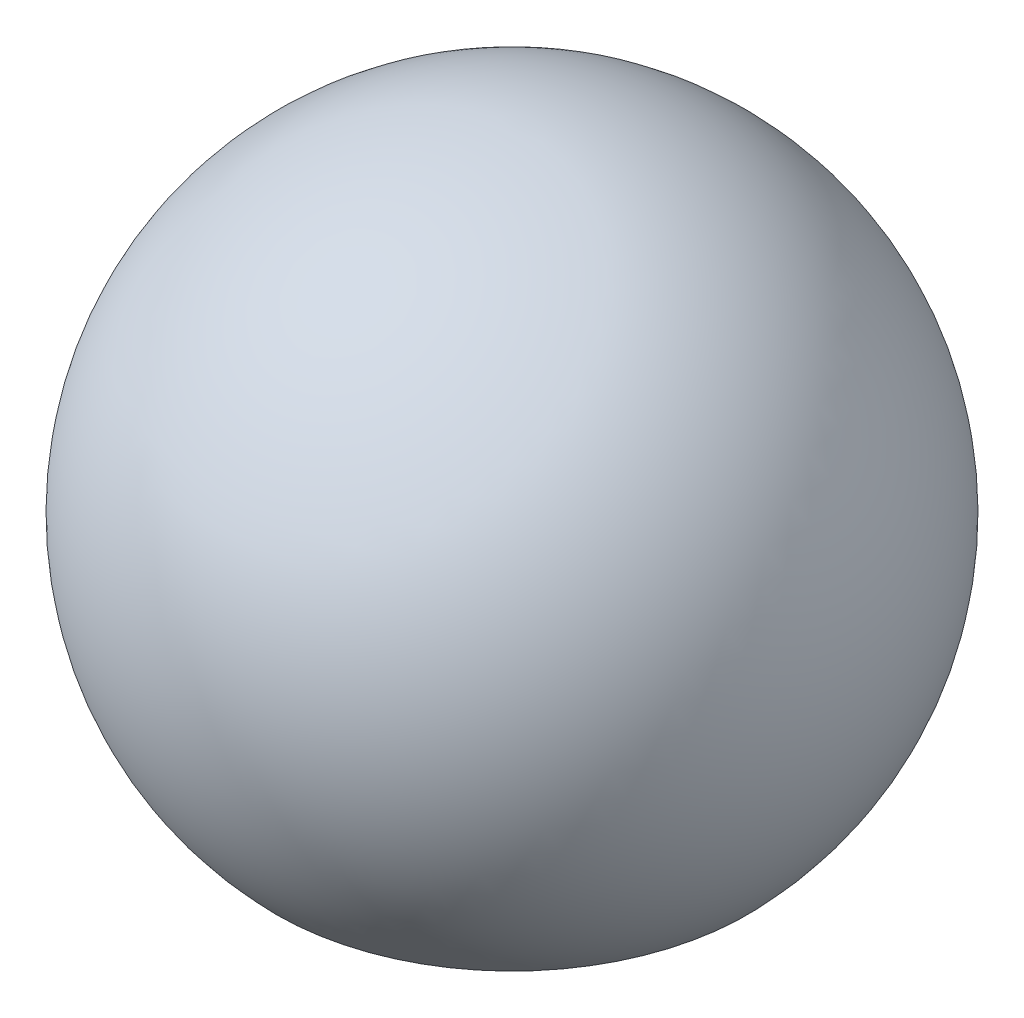
SolidWorks part; units mm, degrees
ref_plane "Front Plane" through (0, 0, 0) normal (0, 0, 1) x (1, 0, 0)
ref_plane "Top Plane" through (0, 0, 0) normal (0, 1, 0) x (1, 0, 0)
ref_plane "Right Plane" through (0, 0, 0) normal (1, 0, 0) x (0, 0, -1)
sketch "Sketch1" plane through (0, 0, 0) normal (0, 1, 0) x (1, 0, 0)
  line L0 (31.5004, 88.2413) -> (31.5004, 80.2413)
  arc A0 (31.5004, 88.2413) -> (31.5004, 80.2413) centre (31.5004, 84.2413) ccw
  dimension "D1" = 8
revolve "Revolve1" add sketch "Sketch1" angle 360 about L0
sketch "Sketch2" plane through (0, 0, 0) normal (0, 1, 0) x (1, 0, 0)
  circle A0 centre (31.5004, 84.2413) radius 0.9474
extrude "Cut-Extrude1" cut sketch "Sketch2" against normal blind 10
ref_plane "Plane1" through (0, -2.8, 0) normal (0, -1, 0) x (-1, 0, 0)
sketch "Sketch3" plane through (0, -2.8, 0) normal (0, -1, 0) x (-1, 0, 0)
  circle A0 centre (-31.5004, 84.2413) radius 6.1126
extrude "Cut-Extrude2" cut sketch "Sketch3" along normal blind 3
